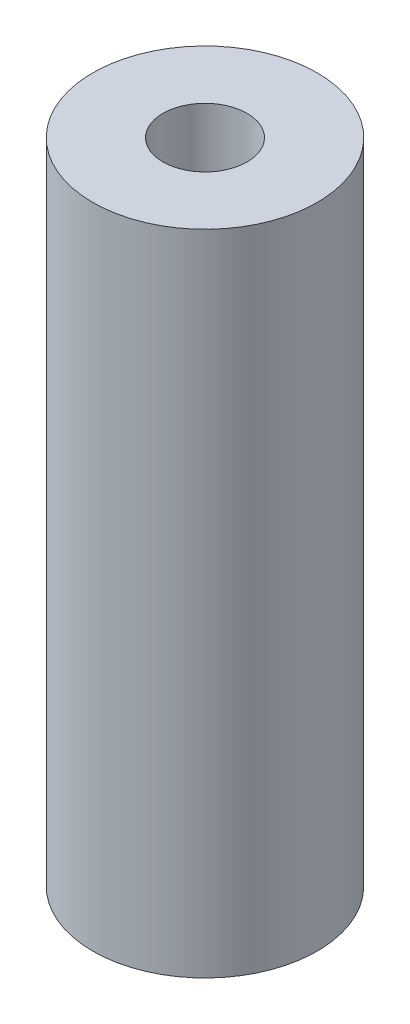
SolidWorks part; units mm, degrees
material "ASTM A36 Steel"
ref_plane "Front Plane" through (0, 0, 0) normal (0, 0, 1) x (1, 0, 0)
ref_plane "Top Plane" through (0, 0, 0) normal (0, 1, 0) x (1, 0, 0)
ref_plane "Right Plane" through (0, 0, 0) normal (1, 0, 0) x (0, 0, -1)
sketch "Sketch1" plane through (0, 0, 0) normal (0, 1, 0) x (1, 0, 0)
  circle A0 centre (0, 0) radius 12.7
  circle A1 centre (0, 0) radius 4.7625
  dimension "D1" = 25.4
  dimension "D2" = 9.525
extrude "Boss-Extrude1" add sketch "Sketch1" along normal mid plane 73.3552
